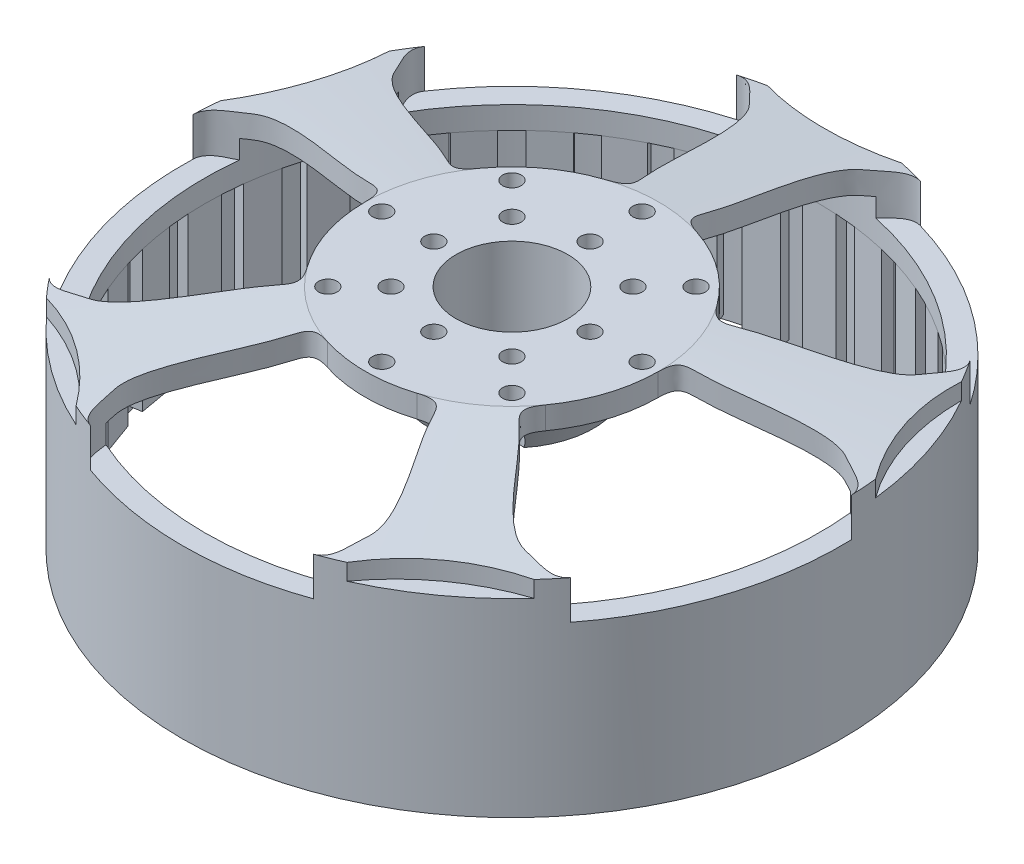
SolidWorks part; units mm, degrees
ref_plane "Ebene vorne" through (0, 0, 0) normal (0, 0, 1) x (1, 0, 0)
ref_plane "Ebene oben" through (0, 0, 0) normal (0, 1, 0) x (1, 0, 0)
ref_plane "Ebene rechts" through (0, 0, 0) normal (1, 0, 0) x (0, 0, -1)
sketch "Skizze1" plane through (0, 0, 0) normal (0, 1, 0) x (1, 0, 0)
  circle A0 centre (0, 0) radius 44.3
  dimension "D1" = 88.6
extrude "Aufsatz-Linear austragen1" add sketch "Skizze1" against normal blind 30.5
sketch "Skizze2" plane through (0, 0, 0) normal (0, 1, 0) x (1, 0, 0)
  circle A0 centre (0, 0) radius 14
  dimension "D1" = 28
extrude "Aufsatz-Linear austragen2" add sketch "Skizze2" along normal blind 4
chamfer "Fase1" distance 2.8 angle 83.5 1 edges at (0, 0, 44.3)
shell "Wandung1" thickness 3
sketch "Skizze3" plane through (0, 0, 0) normal (0, 1, 0) x (1, 0, 0)
  line L0 (0, 0) -> (0, -48.6706) construction
  line L1 (12.8186, -62.1877) -> (21.1643, -11.7751) construction
  line L2 (28.768, -53.7781) -> (-3.8637, 2.7417) construction
  arc A0 (-6, -18.79) -> (6, -18.79) centre (0, 0) ccw
  circle A1 centre (0, 0) radius 19.7247 construction
  circle A2 centre (0, 0) radius 44.3 construction
  arc A3 (15, -41.6832) -> (-15, -41.6832) centre (0, 0) cw
  spline S0 degree 3 poles (6, -18.79) (9.0007, -17.8318) (8.8566, -19.3902) (13.243, -26.8021) (17.7651, -33.5431) (16.7083, -38.1295) (16.6937, -41.0737) (15, -41.6832) knots 0 0 0 0 0.318772 0.399981 0.766303 0.830883 1 1 1 1
  spline S1 degree 3 poles (-6, -18.79) (-9.0007, -17.8318) (-8.8566, -19.3902) (-13.243, -26.8021) (-17.7651, -33.5431) (-16.7083, -38.1295) (-16.6937, -41.0737) (-15, -41.6832) knots 0 0 0 0 0.318772 0.399981 0.766303 0.830883 1 1 1 1
  dimension "D4" = 28.5
  dimension "D5" = 16.5
  dimension "D7" = 26.5
  dimension "D8" = 30
  dimension "D9" = 6
  dimension "D10" = 10.5
  dimension "D1" = 17
  dimension "D2" = 15
  dimension "D3" = 6
  dimension "D6" = 9.4
extrude "Schnitt-Linear austragen1" cut sketch "Skizze3" against normal blind 8
pattern_circular "Kreismuster1" count 5 over 360 about axis through (0, 0, 0) along (0, 1, 0) of "Schnitt-Linear austragen1"
sketch "Skizze4" plane through (0, 0, 0) normal (0, 1, 0) x (1, 0, 0)
  line L1 (0, 0) -> (0, 61.4469) construction
  arc A2 (-9, 43.3761) -> (9, 43.3761) centre (0, 0) cw
  arc A3 (-9, 43.3761) -> (9, 43.3761) centre (0, 70.9442) ccw
  dimension "D3" = 44.3
  dimension "D5" = 58
  dimension "D4" = 18
extrude "Schnitt-Linear austragen2" cut sketch "Skizze4" against normal blind 5
pattern_circular "Kreismuster2" count 5 over 360 about axis through (0, 0, 0) along (0, 1, 0) of "Schnitt-Linear austragen2"
ref_plane "Ebene1" through (0, -30.5, 0) normal (0, -1, 0) x (-1, 0, 0)
sketch "Skizze5" plane through (0, -30.5, 0) normal (0, -1, 0) x (-1, 0, 0)
  circle A0 centre (0, 0) radius 42.8
  circle A1 centre (0, 0) radius 41.3
  dimension "D1" = 1.5
  dimension "D2" = 82.6
extrude "Schnitt-Linear austragen3" cut sketch "Skizze5" against normal offset from surface (19.5 mm away) 3 up to face at (-39.3705, -8, 12.2964)
sketch "Skizze6" plane through (0, -11, 0) normal (0, -1, 0) x (-1, 0, 0)
  line L0 (0, 0) -> (0, 52.5565) construction
  line L1 (-2.25, 41.3) -> (2.25, 41.3)
  line L2 (-2.25, 41.3) -> (-2.25, 42.8)
  line L3 (-2.25, 42.8) -> (2.25, 42.8)
  line L4 (0, 41.3) -> (0, 42.8)
  line L5 (-2.25, 41.3) -> (0, 42.8) construction
  line L6 (-2.25, 42.8) -> (0, 41.3) construction
  line L7 (2.25, 41.3) -> (2.25, 42.8)
  circle A0 centre (0, 0) radius 42.8 construction
  point P0 (-1.125, 42.05)
  circle M5 centre (0, 0) radius 42.8
  dimension "D1" = 2.25
  dimension "D2" = 1.5
extrude "Aufsatz-Linear austragen3" add sketch "Skizze6" along normal offset from surface (19 mm away) 0.5 contours L1 L7 L4 M5 | L1 L4 L2 M5 up to face at (0, -30.5, -42.8)
pattern_circular "Kreismuster3" count 36 over 360 about axis through (0, 0, 0) along (0, 1, 0) of "Aufsatz-Linear austragen3"
sketch "Skizze7" plane through (0, 4, 0) normal (0, 1, 0) x (1, 0, 0)
  circle A0 centre (0, 0) radius 14
  dimension "D1" = 28
extrude "Schnitt-Linear austragen4" cut sketch "Skizze7" against normal up to surface (4 mm away) up to face at (0, 0, 0)
sketch "Skizze8" plane through (0, 0, 0) normal (0, 0, 1) x (1, 0, 0)
  line L0 (-11, 0) -> (-7.5, 0)
  line L1 (11, 0) -> (-11, 0) construction
  line L2 (-6.1904, 0) -> (-15.8986, 0) construction
  line L3 (-7.5, 0) -> (-7.5, -11)
  line L4 (-7.5, -11) -> (-11, -11)
  line L5 (-11, -11) -> (-15, -3)
  line L6 (-15, -3) -> (-11, -3)
  line L7 (-19.5544, -3) -> (19.5544, -3) construction
  line L8 (-11, -3) -> (11, -3) construction
  line L9 (-11, -3) -> (-11, 0)
  line L10 (0, 2.7799) -> (0, -17.0276) construction
  dimension "D1" = 7.5
  dimension "D2" = 11
  dimension "D3" = 11
  dimension "D4" = 4
  dimension "D5" = 8
revolve "Rotation1" add sketch "Skizze8" angle 360 about L10
hole_wizard "M3 Gewindebohrung1" positions "Skizze10" profile "Skizze9" tap size "M3" standard "ISO" end condition up to next
sketch "Skizze10" plane through (0, 0, 0) normal (0, 1, 0) x (1, 0, 0)
  line L0 (0, 20.2806) -> (0, -0.597) construction
  point P0 (0, 17.5)
  dimension "D1" = 17.5
sketch "Skizze9" plane through (0, 0, -17.5) normal (1, 0, 0) x (0, 0, 1)
  line L0 (0, 0) -> (0, 3.001)
  line L1 (0, 3.001) -> (1.25, 3.001)
  line L2 (1.25, 3.001) -> (1.25, 0)
  line L5 (1.25, 0) -> (0, 0)
  line L11 (0, -6.35) -> (0, 107.95) construction
  dimension "Bohrerdurchmesser" = 2.5
  dimension "Bohrungstiefe" = 3.001
cosmetic thread "Bohrungsgewinde1" parameters "D2"=3
pattern_circular "Kreismuster4" count 8 over 360 about axis through (0, 0, 0) along (0, 1, 0) of "M3 Gewindebohrung1"
hole_wizard "M3 Gewindebohrung2" positions "Skizze12" profile "Skizze11" tap size "M3" standard "ISO"
sketch "Skizze12" plane through (0, 0, 0) normal (0, 1, 0) x (1, 0, 0)
  line L0 (0, -1.0023) -> (0, 15.2646) construction
  point P0 (0, 10.5)
  dimension "D1" = 10.5
sketch "Skizze11" plane through (0, 0, -10.5) normal (1, 0, 0) x (0, 0, 1)
  line L0 (0, 0) -> (0, 8.7511)
  line L1 (0, 8.7511) -> (1.25, 8)
  line L2 (1.25, 8) -> (1.25, 0)
  line L5 (1.25, 0) -> (0, 0)
  line L10 (0, 8.7511) -> (-1.25, 8) construction
  line L11 (0, -6.35) -> (0, 107.95) construction
  dimension "Bohrerdurchmesser" = 2.5
  dimension "Bohrungstiefe" = 8
  dimension "Spitzenwinkel" = 118
cosmetic thread "Bohrungsgewinde2" parameters "D1"=6, "D2"=3
pattern_circular "Kreismuster5" count 4 over 360 about axis through (0, 0, 0) along (0, 1, 0) of "M3 Gewindebohrung2"
hole_wizard "M3 Gewindebohrung3" positions "Skizze14" profile "Skizze13" tap size "M3" standard "ISO"
sketch "Skizze14" plane through (0, 0, 0) normal (0, 1, 0) x (1, 0, 0)
  line L0 (-13.5245, 0) -> (0, 0) construction
  line L1 (0, 0) -> (-8.1317, 8.1317) construction
  point P0 (-8.1317, 8.1317)
  dimension "D1" = 45
  dimension "D2" = 11.5
sketch "Skizze13" plane through (-8.1317, 0, -8.1317) normal (1, 0, 0) x (0, 0, 1)
  line L0 (0, 0) -> (0, 12.2511)
  line L1 (0, 12.2511) -> (1.25, 11.5)
  line L2 (1.25, 11.5) -> (1.25, 0)
  line L5 (1.25, 0) -> (0, 0)
  line L10 (0, 12.2511) -> (-1.25, 11.5) construction
  line L11 (0, -6.35) -> (0, 107.95) construction
  dimension "Bohrerdurchmesser" = 2.5
  dimension "Bohrungstiefe" = 11.5
  dimension "Spitzenwinkel" = 118
cosmetic thread "Bohrungsgewinde3" parameters "D1"=11, "D2"=3
pattern_circular "Kreismuster6" count 4 over 360 about axis through (0, 0, 0) along (0, 1, 0) of "M3 Gewindebohrung3"
